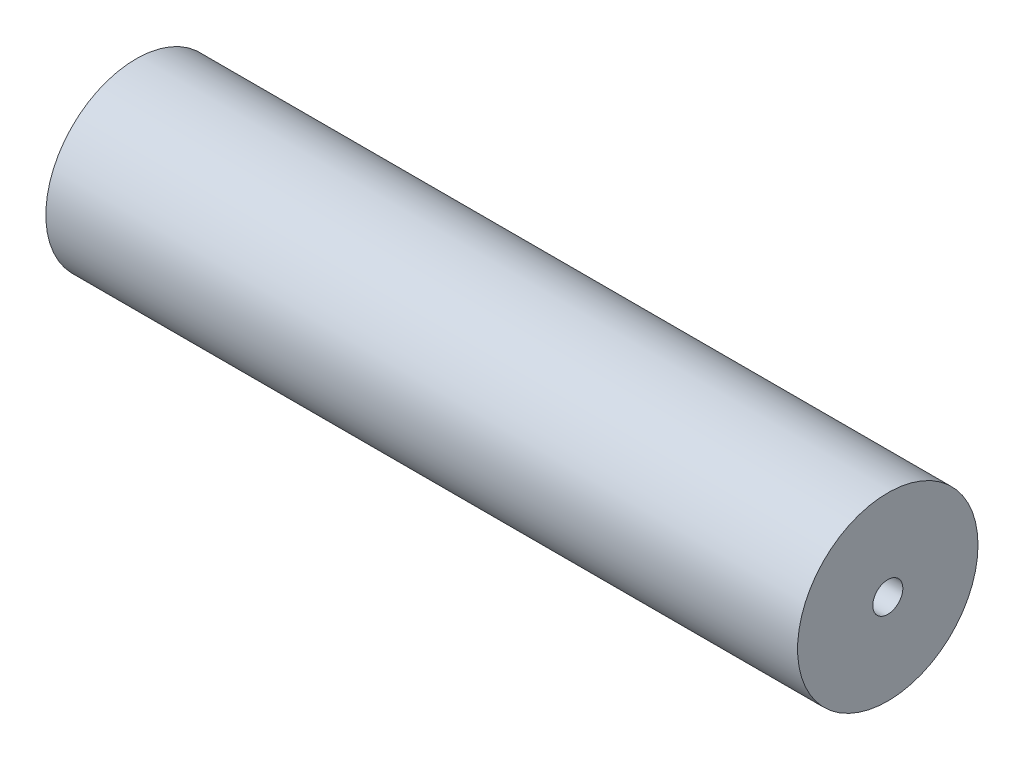
SolidWorks part; units mm, degrees
ref_plane "Front Plane" through (0, 0, 0) normal (0, 0, 1) x (1, 0, 0)
ref_plane "Top Plane" through (0, 0, 0) normal (0, 1, 0) x (1, 0, 0)
ref_plane "Right Plane" through (0, 0, 0) normal (1, 0, 0) x (0, 0, -1)
sketch "Sketch2" plane through (0, 0, 0) normal (1, 0, 0) x (0, 0, -1)
  circle A0 centre (0, 0) radius 30
  circle A1 centre (0, 0) radius 5
  dimension "D1" = 60
  dimension "D2" = 10
extrude "Boss-Extrude1" add sketch "Sketch2" along normal blind 250
